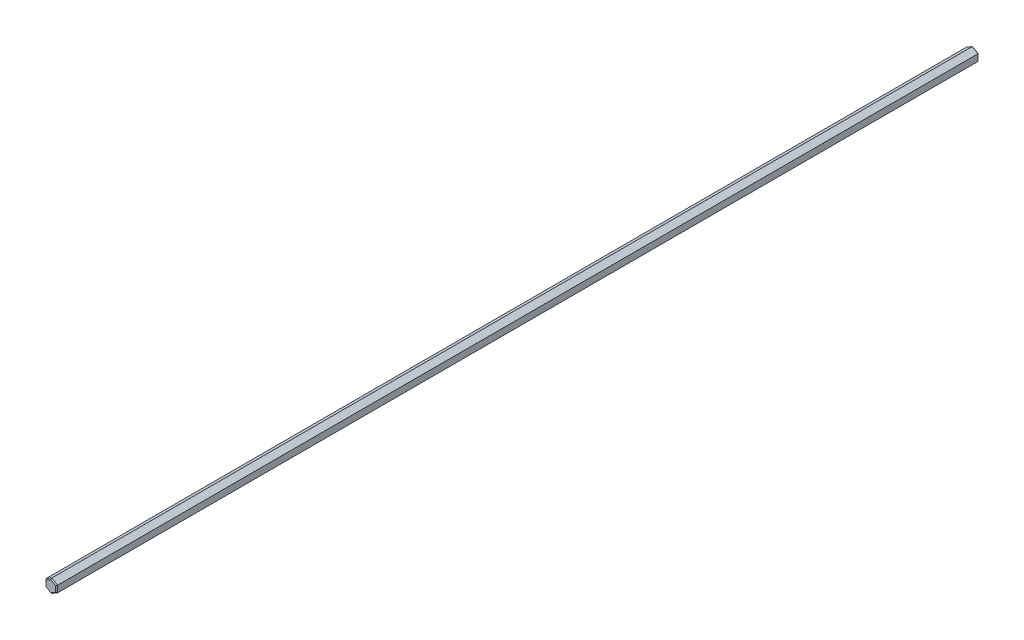
SolidWorks part; units mm, degrees
material "Plain Carbon Steel"
ref_plane "Front Plane" through (0, 0, 0) normal (0, 0, 1) x (1, 0, 0)
ref_plane "Top Plane" through (0, 0, 0) normal (0, 1, 0) x (1, 0, 0)
ref_plane "Right Plane" through (0, 0, 0) normal (1, 0, 0) x (0, 0, -1)
ref_plane "Plane1" through (0, 0, 400) normal (0, 0, 1) x (1, 0, 0)
sketch "Sketch1" plane through (0, 0, 400) normal (0, 0, 1) x (1, 0, 0)
  line L0 (0, -2.8868) -> (2.5, -1.4434)
  line L1 (2.5, -1.4434) -> (2.5, 1.4434)
  line L2 (2.5, 1.4434) -> (0, 2.8868)
  line L3 (0, 2.8868) -> (-2.5, 1.4434)
  line L4 (-2.5, 1.4434) -> (-2.5, -1.4434)
  line L5 (-2.5, -1.4434) -> (0, -2.8868)
extrude "Boss-Extrude1" add sketch "Sketch1" against normal blind 400
chamfer "Chamfer1" distance 0.4 angle 45 12 edges at (-2.5, 0, 0) (-1.25, -2.1651, 0) (-1.25, 2.1651, 0) (1.25, -2.1651, 0) (1.25, 2.1651, 0) (2.5, 0, 0) (-1.25, 2.1651, 400) (-2.5, 0, 400) (1.25, 2.1651, 400) (-1.25, -2.1651, 400) (2.5, 0, 400) (1.25, -2.1651, 400)
